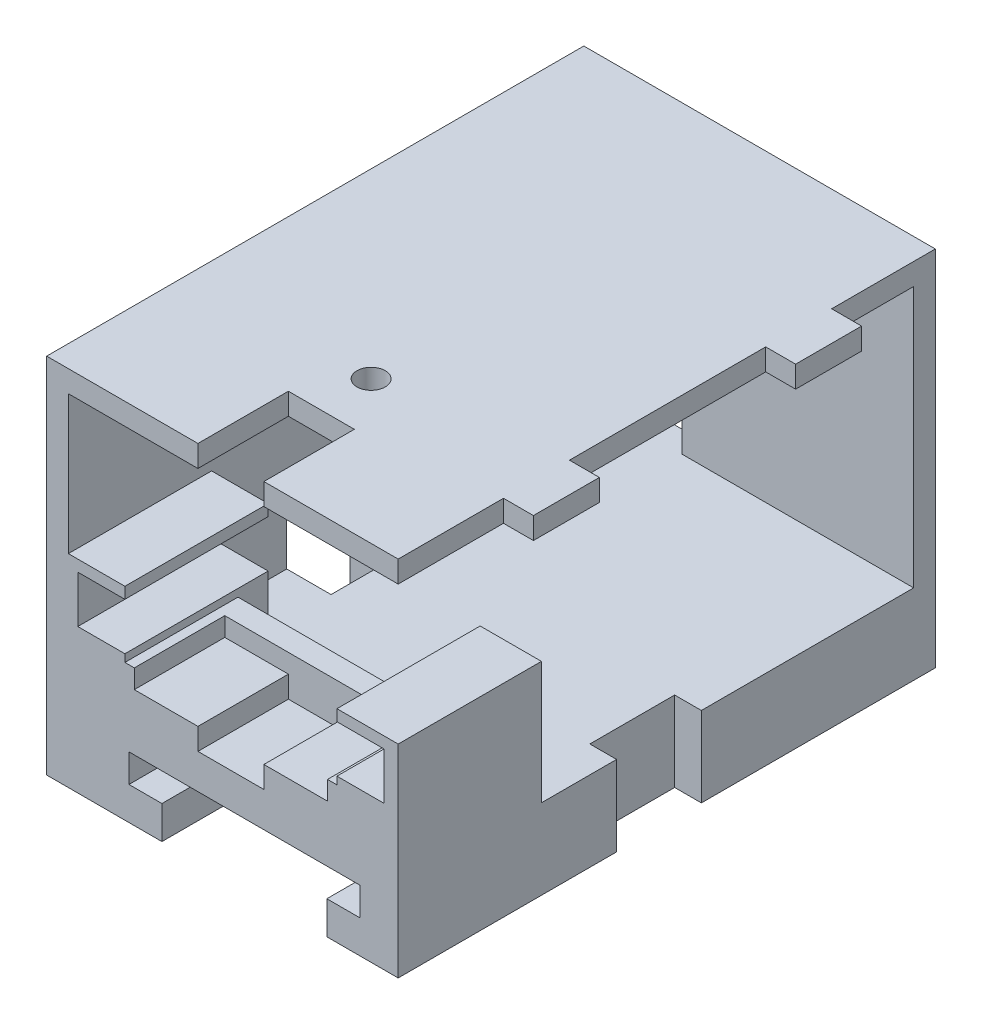
SolidWorks part; units mm, degrees
ref_plane "Front Plane" through (0, 0, 0) normal (0, 0, 1) x (1, 0, 0)
ref_plane "Top Plane" through (0, 0, 0) normal (0, 1, 0) x (1, 0, 0)
ref_plane "Right Plane" through (0, 0, 0) normal (1, 0, 0) x (0, 0, -1)
ref_plane "Plane3" through (0, 0, 53.83) normal (0, 0, 1) x (1, 0, 0)
sketch "Sketch1" plane through (0, 0, 0) normal (1, 0, 0) x (0, 0, -1)
  line L0 (0, 40.694) -> (0, 2.194)
  line L1 (0, 1.7462) -> (0, -1.7462) construction
  line L8 (-53.825, 2.194) -> (-53.825, 40.694)
  line L13 (-53.825, 40.694) -> (0, 40.694)
  line L19 (-53.825, 2.194) -> (0, 2.194)
  dimension "D1" = 0
extrude "main extrude" add sketch "Sketch1" along normal blind 2.3
sketch "Sketch3" plane through (2.3, 0, 0) normal (1, 0, 0) x (0, 0, -1)
  line L4 (-2.3, 38.394) -> (-2.3, 10.694)
  line L8 (-53.825, 38.394) -> (-2.3, 38.394)
  line L13 (-53.825, 40.694) -> (-53.825, 38.394)
  line L14 (-53.825, 40.694) -> (0, 40.694)
  line L15 (0, 40.694) -> (0, 2.194)
  line L16 (0, 2.194) -> (-53.825, 2.194)
  line L19 (-53.825, 10.694) -> (-2.3, 10.694)
  line L20 (-53.825, 40.694) -> (-53.825, 2.194) construction
  line L22 (-53.825, 10.694) -> (-53.825, 2.194)
  dimension "D1" = 2.3
  dimension "D2" = 2.3
extrude "walls" add sketch "Sketch3" along normal blind 35
sketch "Sketch36" plane through (0, 0, 53.825) normal (0, 0, 1) x (1, 0, 0)
  line L0 (37.3, 40.694) -> (0, 40.694) construction
  line L1 (8, 40.694) -> (15, 40.694)
  line L2 (8, 40.694) -> (8, 38.394)
  line L3 (8, 38.394) -> (15, 38.394)
  line L4 (15, 40.694) -> (15, 38.394)
  line L5 (37.3, 38.394) -> (2.3, 38.394) construction
  line L6 (37.3, 38.394) -> (2.3, 38.394) construction
  line L7 (23, 40.694) -> (30, 40.694)
  line L8 (23, 40.694) -> (23, 38.394)
  line L9 (23, 38.394) -> (30, 38.394)
  line L10 (30, 40.694) -> (30, 38.394)
  line L11 (0, 40.694) -> (0, 2.194) construction
  line L12 (0, 32.694) -> (2.3, 32.694)
  line L13 (0, 32.694) -> (0, 25.694)
  line L14 (0, 25.694) -> (2.3, 25.694)
  line L15 (2.3, 32.694) -> (2.3, 25.694)
  line L16 (2.3, 38.394) -> (2.3, 10.694) construction
  line L17 (2.3, 38.394) -> (2.3, 10.694) construction
  line L18 (0, 17.694) -> (2.3, 17.694)
  line L19 (0, 17.694) -> (0, 10.694)
  line L20 (0, 10.694) -> (2.3, 10.694)
  line L21 (2.3, 17.694) -> (2.3, 10.694)
  dimension "D1" = 8
  dimension "D2" = 8
  dimension "D3" = 7
  dimension "D4" = 7
  dimension "D5" = 7
  dimension "D6" = 7
  dimension "D7" = 8
  dimension "D8" = 8
extrude "Puzzle (main walls)" add sketch "Sketch36" along normal blind 3.175
sketch "Sketch25" plane through (0, 0, 2.3) normal (0, 0, 1) x (1, 0, 0)
  line L1 (2.3, 10.694) -> (12.703, 10.694)
  line L2 (2.3, 10.694) -> (2.3, 17.2991)
  line L3 (2.3, 17.2991) -> (12.703, 17.2991)
  line L4 (12.703, 10.694) -> (12.703, 17.2991)
extrude "Wire Hole" cut sketch "Sketch25" against normal through all
sketch "Sketch19" plane through (0, 10.694, 0) normal (0, 1, 0) x (1, 0, 0)
  line L16 (37.3, -41.8) -> (37.3, -53.825)
  line L18 (30.8, -53.825) -> (37.3, -53.825)
  line L27 (37.3, 0) -> (37.3, -53.825) construction
  line L40 (30.8, -53.825) -> (30.8, -41.8)
  line L41 (30.8, -41.8) -> (37.3, -41.8)
  line L47 (2.3, -53.825) -> (8.3, -53.825)
  line L48 (2.3, -53.825) -> (2.3, -41.8)
  line L49 (2.3, -41.8) -> (8.3, -41.8)
  line L50 (8.3, -53.825) -> (8.3, -41.8)
extrude "IR mount" add sketch "Sketch19" along normal blind 7
sketch "Sketch24" plane through (0, 0, 53.83) normal (0, 0, 1) x (1, 0, 0)
  line L0 (37.3, 2.194) -> (0, 2.194) construction
  line L1 (12.23, 2.194) -> (29.73, 2.194)
  line L2 (12.23, 2.194) -> (12.23, 5.694)
  line L4 (29.73, 2.194) -> (29.73, 5.694)
  line L5 (12.23, 5.694) -> (8.73, 5.694)
  line L6 (8.73, 5.694) -> (8.73, 8.694)
  line L9 (33.23, 8.694) -> (33.23, 5.694)
  line L10 (33.23, 5.694) -> (29.73, 5.694)
  line L11 (0, 10.694) -> (0, 2.194) construction
  line L12 (8.73, 8.694) -> (33.23, 8.694)
  dimension "D1" = 8.73
  dimension "D2" = 0
  dimension "D3" = 3.5
  dimension "D4" = 3
  dimension "D5" = 3
  dimension "D6" = 3.5
  dimension "D7" = 3.5
  dimension "D8" = 3.5
  dimension "D9" = 17.5
extrude "Magnet Mount Hole" cut sketch "Sketch24" against normal blind 51.83
sketch "Sketch40" plane through (0, 40.694, 0) normal (0, 1, 0) x (1, 0, 0)
  line L0 (37.3, 0) -> (37.3, -53.825) construction
  line L1 (0, 0) -> (0, -53.825) construction
  circle A0 centre (19.3, -41.8726) radius 1.5
  dimension "D1" = 3
  dimension "D2" = 18
  dimension "D3" = 19.3
extrude "LED Space" cut sketch "Sketch40" against normal blind 3
sketch "Sketch42" plane through (37.3, 0, 0) normal (1, 0, 0) x (0, 0, -1)
  line L0 (0, 40.694) -> (-53.825, 40.694) construction
  line L1 (-45.825, 40.694) -> (-38.825, 40.694)
  line L2 (-45.825, 40.694) -> (-45.825, 38.394)
  line L3 (-45.825, 38.394) -> (-38.825, 38.394)
  line L4 (-38.825, 40.694) -> (-38.825, 38.394)
  line L5 (-53.825, 38.394) -> (-2.3, 38.394) construction
  line L6 (-53.825, 38.394) -> (-2.3, 38.394) construction
  line L7 (-18, 40.694) -> (-11, 40.694)
  line L8 (-18, 40.694) -> (-18, 38.394)
  line L9 (-18, 38.394) -> (-11, 38.394)
  line L10 (-11, 40.694) -> (-11, 38.394)
  line L11 (-53.825, 40.694) -> (-53.825, 38.394) construction
  line L12 (0, 2.194) -> (0, 40.694) construction
  dimension "D1" = 8
  dimension "D2" = 7
  dimension "D3" = 7
  dimension "D4" = 11
extrude "Boss-Extrude15" add sketch "Sketch42" along normal blind 3.175
sketch "Sketch44" plane through (0, 17.694, 0) normal (0, 1, 0) x (1, 0, 0)
  line L1 (2.3, -41.8) -> (8.3, -41.8)
  line L2 (2.3, -41.8) -> (2.3, -53.825)
  line L3 (2.3, -53.825) -> (8.3, -53.825)
  line L4 (8.3, -41.8) -> (8.3, -53.825)
  line L5 (30.8, -41.8) -> (37.3, -41.8)
  line L6 (30.8, -41.8) -> (30.8, -53.825)
  line L7 (30.8, -53.825) -> (37.3, -53.825)
  line L8 (37.3, -41.8) -> (37.3, -53.825)
extrude "Boss-Extrude16" add sketch "Sketch44" along normal blind 6
sketch "Sketch45" plane through (0, 0, 53.825) normal (0, 0, 1) x (1, 0, 0)
  line L0 (30.8, 23.694) -> (30.8, 10.694) construction
  line L1 (30.8, 22.494) -> (35.8, 22.494)
  line L2 (30.8, 22.494) -> (30.8, 17.494)
  line L3 (30.8, 17.494) -> (35.8, 17.494)
  line L4 (35.8, 22.494) -> (35.8, 17.494)
  line L5 (8.3, 23.694) -> (8.3, 10.694) construction
  line L6 (8.3, 22.494) -> (3.3, 22.494)
  line L7 (8.3, 22.494) -> (8.3, 17.494)
  line L8 (8.3, 17.494) -> (3.3, 17.494)
  line L9 (3.3, 22.494) -> (3.3, 17.494)
  line L10 (2.3, 23.694) -> (8.3, 23.694) construction
  line L11 (30.8, 23.694) -> (37.3, 23.694) construction
  dimension "D1" = 1.2
  dimension "D2" = 1.2
  dimension "D3" = 5
  dimension "D4" = 5
  dimension "D5" = 5
  dimension "5" = 5
extrude "IR placement" cut sketch "Sketch45" against normal up to surface (12.025 mm away) up to face at (5.3, 17.194, 41.8)
sketch "Sketch47" plane through (0, 0, 0) normal (0, 0, -1) x (-1, 0, 0)
  circle A0 centre (-21.019, 5.2627) radius 2.5
  dimension "D1" = 5
extrude "Cut-Extrude2" cut sketch "Sketch47" against normal up to surface (2 mm away) up to face at (20.98, 5.569, 2)
sketch "Sketch48" plane through (0, 2.194, 0) normal (0, -1, 0) x (1, 0, 0)
  line L0 (0, 53.825) -> (0, 0) construction
  line L1 (0, 33.825) -> (7, 33.825)
  line L2 (0, 33.825) -> (0, 24.825)
  line L3 (0, 24.825) -> (7, 24.825)
  line L4 (7, 33.825) -> (7, 24.825)
  line L5 (34.4625, 33.825) -> (41.4625, 33.825)
  line L6 (34.4625, 33.825) -> (34.4625, 24.825)
  line L7 (34.4625, 24.825) -> (41.4625, 24.825)
  line L8 (41.4625, 33.825) -> (41.4625, 24.825)
  line L9 (37.3, 53.825) -> (29.73, 53.825) construction
  line L10 (12.23, 53.825) -> (0, 53.825) construction
  dimension "D1" = 20
  dimension "D2" = 20
  dimension "D3" = 9
extrude "Cut-Extrude3" cut sketch "Sketch48" against normal blind 15
sketch "Sketch50" plane through (0, 0, 53.825) normal (0, 0, 1) x (1, 0, 0)
  line L0 (37.3, 38.394) -> (2.3, 38.394)
  line L1 (0, 40.694) -> (37.3, 40.694)
  line L4 (37.3, 40.694) -> (37.3, 38.394)
  line L5 (2.3, 38.394) -> (2.3, 23.694)
  line L6 (2.3, 23.694) -> (8.3, 23.694)
  line L7 (8.3, 23.694) -> (8.3, 22.494)
  line L8 (8.3, 23.694) -> (8.3, 22.494) construction
  line L9 (8.3, 22.494) -> (3.3, 22.494)
  line L10 (3.3, 22.494) -> (3.3, 17.494)
  line L11 (3.3, 17.494) -> (8.3, 17.494)
  line L12 (8.3, 17.494) -> (8.3, 10.694)
  line L13 (8.3, 10.694) -> (30.8, 10.694)
  line L14 (30.8, 10.694) -> (30.8, 17.494)
  line L15 (30.8, 17.494) -> (30.8, 10.694) construction
  line L16 (30.8, 17.494) -> (35.8, 17.494)
  line L17 (35.8, 17.494) -> (35.8, 22.494)
  line L18 (30.8, 23.694) -> (37.3, 23.694)
  line L20 (30.8, 23.694) -> (30.8, 22.494)
  line L21 (30.8, 23.694) -> (30.8, 22.494) construction
  line L23 (29.73, 2.194) -> (29.73, 5.694)
  line L24 (29.73, 5.694) -> (33.23, 5.694)
  line L25 (33.23, 5.694) -> (33.23, 8.694)
  line L26 (33.23, 8.694) -> (8.73, 8.694)
  line L27 (8.73, 8.694) -> (8.73, 5.694)
  line L28 (8.73, 5.694) -> (12.23, 5.694)
  line L29 (12.23, 5.694) -> (12.23, 2.194)
  line L30 (0, 40.694) -> (0, 2.194)
  line L31 (37.3, 23.694) -> (37.3, 2.194)
  line L32 (0, 2.194) -> (12.23, 2.194)
  line L33 (29.73, 2.194) -> (37.3, 2.194)
  line L34 (30.8, 22.494) -> (35.8, 22.494)
extrude "Boss-Extrude17" add sketch "Sketch50" along normal blind 3.175
ref_plane "Plane5" through (37.3, 0, 0) normal (1, 0, 0) x (0, 0, -1)
sketch "Sketch6" [suppressed] plane through (0, 0, 53.83) normal (0, 0, 1) x (1, 0, 0)
  line L2 (0, 40.694) -> (0, 2.194)
  line L6 (0, 40.694) -> (40.48, 40.694)
  line L7 (40.48, 40.694) -> (40.48, 2.194)
  line L8 (0, 2.194) -> (40.48, 2.194)
extrude "front lid" [suppressed] add sketch "Sketch6" along normal blind 3.175 separate body
sketch "Sketch7" [suppressed] plane through (0, 0, 57.005) normal (0, 0, 1) x (1, 0, 0)
  line L0 (0, 2.194) -> (40.48, 2.194) construction
  line L6 (0, -21.175) -> (0, 21.175) construction
  line L10 (19.75, 17.854) -> (27.25, 17.854)
  line L11 (19.75, 17.854) -> (12.25, 17.854)
  line L12 (12.25, 17.854) -> (12.25, 32.854)
  line L13 (12.25, 32.854) -> (27.25, 32.854)
  line L14 (27.25, 17.854) -> (27.25, 32.854)
  circle A0 centre (19.75, 25.354) radius 7.5 construction
  point P12 (19.75, 25.354)
  dimension "D1" = 15
  dimension "D2" = 19.75
  dimension "D4" = 15.66
extrude "nosepoke hole" [suppressed] cut sketch "Sketch7" against normal blind 3.175
sketch "Sketch34" [suppressed] plane through (0, 0, 57.005) normal (0, 0, 1) x (1, 0, 0)
  line L0 (0, 40.694) -> (0, 2.194) construction
  line L1 (0, 32.694) -> (2.3, 32.694)
  line L2 (0, 32.694) -> (0, 25.694)
  line L3 (0, 25.694) -> (2.3, 25.694)
  line L4 (2.3, 32.694) -> (2.3, 25.694)
  line L9 (40.48, 40.694) -> (0, 40.694) construction
  line L10 (8, 40.694) -> (15, 40.694)
  line L11 (8, 40.694) -> (8, 38.394)
  line L12 (8, 38.394) -> (15, 38.394)
  line L13 (15, 40.694) -> (15, 38.394)
  line L14 (23, 40.694) -> (30, 40.694)
  line L15 (23, 40.694) -> (23, 38.394)
  line L16 (23, 38.394) -> (30, 38.394)
  line L17 (30, 40.694) -> (30, 38.394)
  line L23 (40.48, 2.194) -> (40.48, 40.694) construction
  line L24 (0, 17.694) -> (2.3, 17.694)
  line L25 (0, 17.694) -> (0, 10.694)
  line L26 (0, 10.694) -> (2.3, 10.694)
  line L27 (2.3, 17.694) -> (2.3, 10.694)
  line L32 (40.48, 32.694) -> (37.305, 32.694)
  line L33 (40.48, 32.694) -> (40.48, 25.694)
  line L34 (40.48, 25.694) -> (37.305, 25.694)
  line L35 (37.305, 32.694) -> (37.305, 25.694)
  line L37 (40.48, 17.694) -> (37.305, 17.694)
  line L38 (40.48, 17.694) -> (40.48, 10.694)
  line L39 (40.48, 10.694) -> (37.305, 10.694)
  line L40 (37.305, 17.694) -> (37.305, 10.694)
  point P16 (15, 39.544)
  dimension "D1" = 8
  dimension "D2" = 8
  dimension "D3" = 8
  dimension "D4" = 8
  dimension "D5" = 8
  dimension "D6" = 7
  dimension "D7" = 7
  dimension "D8" = 2.3
  dimension "D9" = 8
extrude "Puzzle (Front Lid)" [suppressed] cut sketch "Sketch34" against normal up to surface (3.175 mm away)
sketch "Sketch46" [suppressed] plane through (0, 0, 57.005) normal (0, 0, 1) x (1, 0, 0)
  line L0 (12.23, 2.194) -> (29.73, 2.194)
  line L1 (12.23, 2.194) -> (12.23, 5.694)
  line L2 (29.73, 2.194) -> (29.73, 5.694)
  line L3 (12.23, 5.694) -> (8.73, 5.694)
  line L4 (8.73, 5.694) -> (8.73, 8.694)
  line L5 (33.23, 8.694) -> (33.23, 5.694)
  line L6 (33.23, 5.694) -> (29.73, 5.694)
  line L7 (8.73, 8.694) -> (33.23, 8.694)
  line L8 (0, 10.694) -> (0, 2.194) construction
  line L10 (0, 2.194) -> (40.48, 2.194) construction
  dimension "D1" = 8.73
  dimension "D3" = 3
  dimension "D4" = 3.5
  dimension "D5" = 0
  dimension "D6" = 3.5
  dimension "D7" = 3
  dimension "D8" = 3.5
  dimension "D9" = 3.5
  dimension "D10" = 17.5
extrude "magnet mount front lid" [suppressed] cut sketch "Sketch46" against normal up to surface (3.175 mm away)
sketch "Lever Space in Operant (reference)" [suppressed] plane through (0, 0, 57.005) normal (0, 0, 1) x (1, 0, 0)
  line L1 (2.88, 34.514) -> (34.4305, 34.514) construction
  line L2 (2.88, 34.514) -> (2.88, 17.854) construction
  line L3 (2.88, 17.854) -> (34.4305, 17.854) construction
  line L4 (34.4305, 34.514) -> (34.4305, 17.854) construction
  line L7 (0, -21.175) -> (0, 21.175) construction
  line L8 (2.3, 10.694) -> (2.3, 38.394) construction
  line L9 (12.25, 32.854) -> (27.25, 32.854) construction
  line L10 (12.25, 32.854) -> (12.25, 17.854) construction
  line L11 (12.25, 17.854) -> (27.25, 17.854) construction
  line L12 (27.25, 32.854) -> (27.25, 17.854) construction
  line L14 (0, 2.194) -> (40.48, 2.194) construction
  dimension "D1" = 15.66
  dimension "D2" = 2.88
  dimension "D3" = 31.5505
  dimension "D4" = 16.66
ref_plane "contact face with wall" [suppressed] through (0, 0, 57.005) normal (0, 0, 1) x (1, 0, 0)
sketch "Acrylic Guard (reference)" [suppressed] plane through (0, 0, 53.83) normal (0, 0, -1) x (-1, 0, 0)
  line L0 (7.75, 32.854) -> (50007.75, 32.854) construction
  line L1 (-27.25, 32.854) -> (-27.25, 17.854)
  line L2 (-27.25, 17.854) -> (-12.25, 17.854)
  line L3 (-12.25, 17.854) -> (-12.25, 32.854)
  line L4 (-12.25, 32.854) -> (-9.25, 32.854)
  line L5 (-9.25, 32.854) -> (-9.25, 14.854)
  line L6 (-9.25, 14.854) -> (-30.25, 14.854)
  line L7 (-30.25, 14.854) -> (-30.25, 32.854)
  line L8 (-30.25, 32.854) -> (-27.25, 32.854)
  dimension "D1" = 3
sketch "Sketch20" [suppressed] plane through (37.3, 0, 0) normal (1, 0, 0) x (0, 0, -1)
  line L1 (-53.825, 40.694) -> (0, 40.694)
  line L2 (-53.825, 40.694) -> (-53.825, 2.194)
  line L3 (-53.825, 2.194) -> (0, 2.194)
  line L4 (0, 40.694) -> (0, 2.194)
extrude "Side main" [suppressed] add sketch "Sketch20" along normal blind 3.175 separate body
sketch "Sketch37" [suppressed] plane through (0, 0, 53.825) normal (0, 0, 1) x (1, 0, 0)
  line L0 (37.3, 40.694) -> (37.3, 2.194) construction
  line L1 (37.3, 32.694) -> (40.475, 32.694)
  line L2 (37.3, 32.694) -> (37.3, 25.694)
  line L3 (37.3, 25.694) -> (40.475, 25.694)
  line L4 (40.475, 32.694) -> (40.475, 25.694)
  line L5 (40.475, 40.694) -> (40.475, 2.194) construction
  line L6 (40.475, 40.694) -> (37.3, 40.694) construction
  line L7 (37.3, 17.694) -> (40.475, 17.694)
  line L8 (37.3, 17.694) -> (37.3, 10.694)
  line L9 (37.3, 10.694) -> (40.475, 10.694)
  line L10 (40.475, 17.694) -> (40.475, 10.694)
  dimension "D1" = 8
  dimension "D2" = 7
  dimension "D3" = 8
  dimension "D4" = 7
extrude "Puzzle (side part)" [suppressed] add sketch "Sketch37" along normal blind 3.175
sketch "Sketch41" [suppressed] plane through (40.475, 0, 0) normal (1, 0, 0) x (0, 0, -1)
  line L0 (0, 40.694) -> (-53.825, 40.694) construction
  line L1 (-45.825, 40.694) -> (-38.825, 40.694)
  line L2 (-45.825, 40.694) -> (-45.825, 38.394)
  line L3 (-45.825, 38.394) -> (-38.825, 38.394)
  line L4 (-38.825, 40.694) -> (-38.825, 38.394)
  line L5 (-53.825, 40.694) -> (-53.825, 2.194) construction
  line L6 (-18, 40.694) -> (-11, 40.694)
  line L7 (-18, 40.694) -> (-18, 38.394)
  line L8 (-18, 38.394) -> (-11, 38.394)
  line L9 (-11, 40.694) -> (-11, 38.394)
  line L10 (0, 2.194) -> (0, 40.694) construction
  dimension "D1" = 8
  dimension "D2" = 11
  dimension "D3" = 7
extrude "Cut-Extrude1" [suppressed] cut sketch "Sketch41" against normal up to surface (3.175 mm away)
sketch "Sketch49" [suppressed] plane through (0, 2.194, 0) normal (0, -1, 0) x (1, 0, 0)
  line L0 (40.475, 53.825) -> (40.475, 0) construction
  line L1 (40.475, 33.825) -> (33.475, 33.825)
  line L2 (40.475, 33.825) -> (40.475, 24.825)
  line L3 (40.475, 24.825) -> (33.475, 24.825)
  line L4 (33.475, 33.825) -> (33.475, 24.825)
  line L5 (40.475, 53.825) -> (37.3, 53.825) construction
  dimension "D1" = 20
extrude "Cut-Extrude4" [suppressed] cut sketch "Sketch49" against normal blind 15
sketch "Sketch51" plane through (0, 10.694, 0) normal (0, 1, 0) x (1, 0, 0)
  line L0 (8.3, -57) -> (8.3, -41.8) construction
  line L1 (30.8, -57) -> (8.3, -57)
  line L2 (30.8, -57) -> (30.8, -47)
  line L3 (30.8, -47) -> (8.3, -47)
  line L4 (8.3, -57) -> (8.3, -47)
extrude "Boss-Extrude18" add sketch "Sketch51" along normal blind 4
sketch "Sketch52" plane through (0, 10.694, 0) normal (0, 1, 0) x (1, 0, 0)
  line L0 (30.8, -41.8) -> (30.8, -47) construction
  line L1 (9.3, -47.4) -> (29.8, -47.4)
  line L2 (8.3, -47) -> (8.3, -45)
  line L3 (8.3, -45) -> (30.8, -45)
  line L4 (30.8, -47) -> (30.8, -45)
  line L5 (37.3, -57) -> (0, -57) construction
  line L7 (8.3, -47) -> (8.3, -57)
  line L8 (8.3, -57) -> (9.3, -57)
  line L9 (9.3, -47.4) -> (9.3, -57)
  line L12 (30.8, -47) -> (30.8, -57)
  line L13 (30.8, -57) -> (29.8, -57)
  line L14 (29.8, -47.4) -> (29.8, -57)
extrude "Boss-Extrude19" add sketch "Sketch52" along normal blind 6
sketch "Sketch53" [suppressed] plane through (0, 0, 53.825) normal (0, 0, 1) x (1, 0, 0)
  line L1 (37.3, 40.694) -> (40.475, 40.694)
  line L2 (37.3, 40.694) -> (37.3, 2.194)
  line L3 (37.3, 2.194) -> (40.475, 2.194)
  line L4 (40.475, 40.694) -> (40.475, 2.194)
extrude "Boss-Extrude20" [suppressed] add sketch "Sketch53" along normal blind 3.175
sketch "Sketch54" plane through (0, 0, 57) normal (0, 0, 1) x (1, 0, 0)
  line L0 (9.3, 14.694) -> (29.8, 14.694) construction
  line L1 (19.55, 14.694) -> (19.55, 38.394) construction
  line L2 (2.3, 38.394) -> (37.3, 38.394) construction
  line L3 (37.3, 40.694) -> (0, 40.694) construction
  line L4 (16.05, 38.394) -> (23.05, 38.394)
  line L5 (16.05, 38.394) -> (16.05, 40.694)
  line L6 (16.05, 40.694) -> (23.05, 40.694)
  line L7 (23.05, 38.394) -> (23.05, 40.694)
  line L9 (16.05, 14.694) -> (23.05, 14.694)
  line L10 (16.05, 14.694) -> (16.05, 12.394)
  line L11 (16.05, 12.394) -> (23.05, 12.394)
  line L12 (23.05, 14.694) -> (23.05, 12.394)
  dimension "D1" = 3.5
  dimension "D2" = 7
  dimension "D3" = 0
  dimension "D4" = 7
extrude "Cut-Extrude5" cut sketch "Sketch54" against normal blind 9.6
